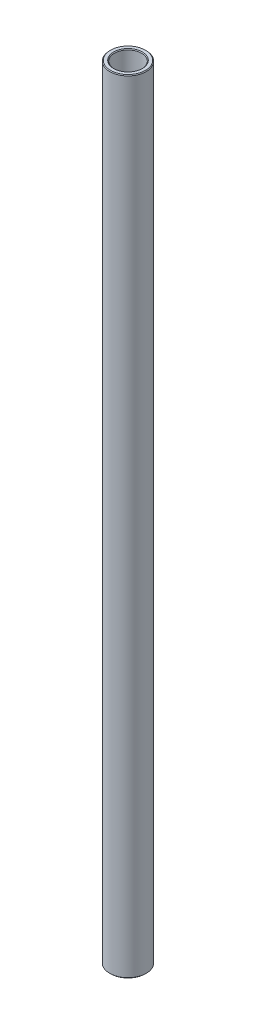
SolidWorks part; units mm, degrees
ref_plane "Front Plane" through (0, 0, 0) normal (0, 0, 1) x (1, 0, 0)
ref_plane "Top Plane" through (0, 0, 0) normal (0, 1, 0) x (1, 0, 0)
ref_plane "Right Plane" through (0, 0, 0) normal (1, 0, 0) x (0, 0, -1)
sketch "Sketch1" plane through (0, 0, 0) normal (0, 0, 1) x (1, 0, 0)
  line L0 (0, 11.6086) -> (0, -11.6086) construction
  line L1 (4.7625, 136.525) -> (6.35, 136.525)
  line L2 (6.35, 136.525) -> (6.35, -136.525)
  line L3 (6.35, -136.525) -> (4.7625, -136.525)
  line L4 (4.7625, -136.525) -> (4.7625, 136.525)
  line L5 (4.7625, 0) -> (0, 0) construction
  dimension "D1" = 9.525
  dimension "D2" = 12.7
  dimension "D3" = 273.05
revolve "Revolve1" add sketch "Sketch1" angle 360 about L0
chamfer "Chamfer1" distance 0.254 angle 45 4 edges at (-4.7625, -136.525, 0) (-6.35, -136.525, 0) (-6.35, 136.525, 0) (-4.7625, 136.525, 0)
